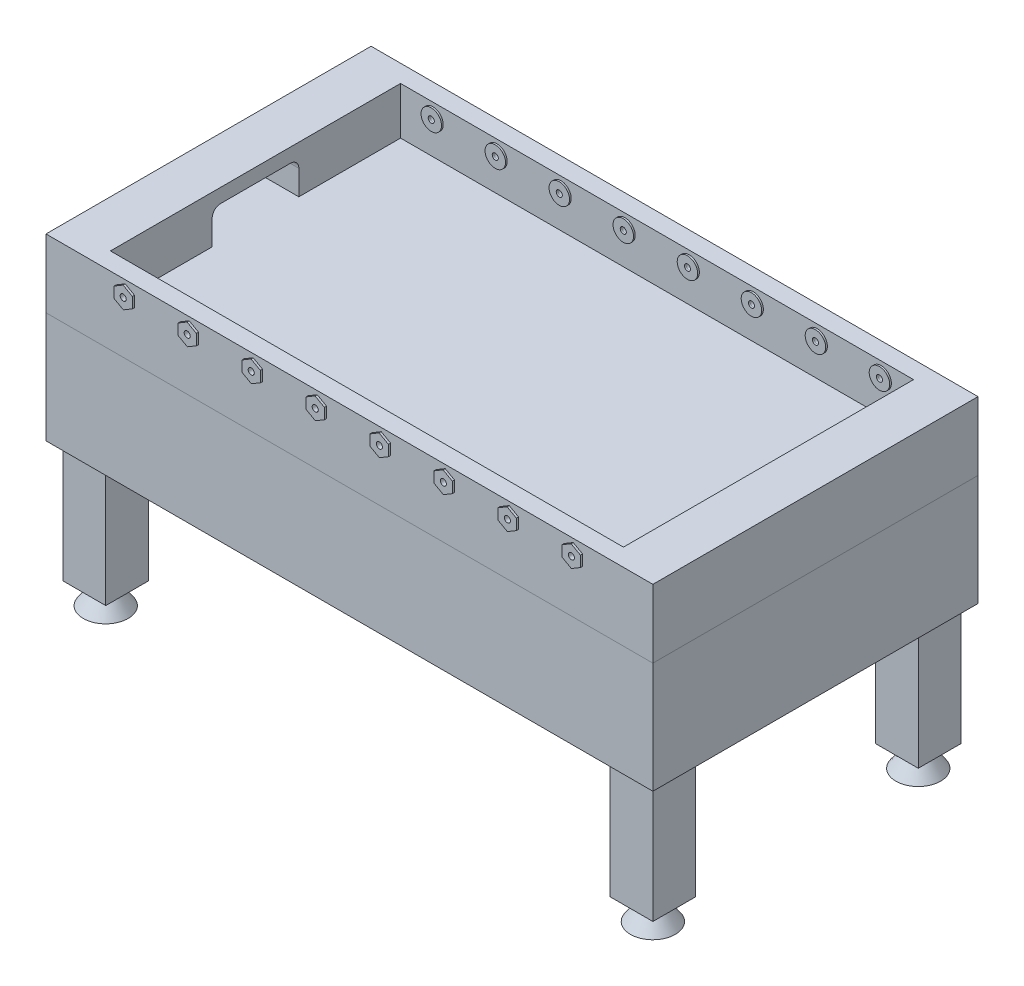
SolidWorks part; units mm, degrees
ref_plane "Front Plane" through (0, 0, 0) normal (0, 0, 1) x (1, 0, 0)
ref_plane "Top Plane" through (0, 0, 0) normal (0, 1, 0) x (1, 0, 0)
ref_plane "Right Plane" through (0, 0, 0) normal (1, 0, 0) x (0, 0, -1)
sketch "스케치1" plane through (0, 0, 0) normal (0, 1, 0) x (1, 0, 0)
  line L1 (711.2, -381) -> (-711.2, -381)
  line L2 (711.2, -381) -> (711.2, 381)
  line L3 (711.2, 381) -> (-711.2, 381)
  line L4 (-711.2, -381) -> (-711.2, 381)
  line L5 (711.2, -381) -> (-711.2, 381) construction
  line L6 (711.2, 381) -> (-711.2, -381) construction
  point P0 (0, 0)
  dimension "D1" = 1422.4
  dimension "D2" = 762
extrude "보스-돌출1" add sketch "스케치1" along normal blind 160
sketch "스케치2" plane through (0, 160, 0) normal (0, 1, 0) x (1, 0, 0)
  line L1 (601.2, -340) -> (-601.2, -340)
  line L2 (601.2, -340) -> (601.2, 340)
  line L3 (601.2, 340) -> (-601.2, 340)
  line L4 (-601.2, -340) -> (-601.2, 340)
  line L5 (601.2, -340) -> (-601.2, 340) construction
  line L6 (601.2, 340) -> (-601.2, -340) construction
  point P0 (0, 0)
  dimension "D1" = 1202.4
  dimension "D2" = 680
extrude "컷-돌출1" cut sketch "스케치2" against normal blind 111
sketch "스케치3" plane through (601.2, 0, 0) normal (-1, 0, 0) x (0, 0, 1)
  line L0 (340, 49) -> (-340, 49) construction
  line L2 (-101.6, 49) -> (-101.6, 127)
  line L3 (-101.6, 127) -> (101.6, 127)
  line L4 (101.6, 49) -> (101.6, 127)
  line L5 (0, 49) -> (101.6, 127) construction
  line L6 (-101.6, 127) -> (0, 49) construction
  line L7 (-148.063, 49) -> (174.1502, 49) construction
  line L8 (-101.6, 49) -> (101.6, 49)
  point P0 (0, 49)
  dimension "D1" = 203.2
extrude "컷-돌출2" cut sketch "스케치3" against normal blind 80
mirror "대칭 복사1" about plane through (0, 0, 0) normal (1, 0, 0) of "컷-돌출2"
sketch "스케치4" plane through (0, 0, -340) normal (0, 0, 1) x (1, 0, 0)
  line L0 (-601.2, 49) -> (601.2, 49) construction
  line L1 (-601.2, 160) -> (-601.2, 49) construction
  line L2 (601.2, 49) -> (601.2, 160) construction
  line L3 (0, -88) -> (0, 88) construction
  circle A0 centre (-525.2, 126.5) radius 24
  circle A1 centre (-375.2, 126.5) radius 24
  circle A2 centre (-225.2, 126.5) radius 24
  circle A3 centre (-75.2, 126.5) radius 24
  circle A4 centre (75.2, 126.5) radius 24
  circle A5 centre (225.2, 126.5) radius 24
  circle A6 centre (375.2, 126.5) radius 24
  circle A7 centre (525.2, 126.5) radius 24
  circle A8 centre (-525.2, 126.5) radius 7.1437
  circle A9 centre (-375.2, 126.5) radius 7.1438
  circle A10 centre (-225.2, 126.5) radius 7.1438
  circle A11 centre (-75.2, 126.5) radius 7.1437
  circle A12 centre (75.2, 126.5) radius 7.1437
  circle A13 centre (225.2, 126.5) radius 7.1438
  circle A14 centre (375.2, 126.5) radius 7.1438
  circle A15 centre (525.2, 126.5) radius 7.1437
  dimension "D3" = 48
  dimension "D4" = 48
  dimension "D6" = 150
  dimension "D8" = 14.2875
  dimension "D9" = 14.2875
  dimension "D10" = 14.2875
  dimension "D11" = 14.2875
  dimension "D1" = 76
  dimension "D2" = 77.5
  dimension "D5" = 150
  dimension "D7" = 150
extrude "보스-돌출2" add sketch "스케치4" along normal blind 4 separate body
mirror "대칭 복사2" about plane through (0, 0, 0) normal (0, 0, 1) of "보스-돌출2"
sketch "스케치5" plane through (0, 0, 0) normal (0, -1, 0) x (1, 0, 0)
  line L1 (711.2, -381) -> (-711.2, -381)
  line L2 (711.2, -381) -> (711.2, 381)
  line L3 (711.2, 381) -> (-711.2, 381)
  line L4 (-711.2, -381) -> (-711.2, 381)
  line L5 (711.2, -381) -> (-711.2, 381) construction
  line L6 (711.2, 381) -> (-711.2, -381) construction
  point P0 (0, 0)
extrude "보스-돌출3" add sketch "스케치5" along normal blind 260 separate body
sketch "스케치6" plane through (0, 0, -340) normal (0, 0, 1) x (1, 0, 0)
  circle A0 centre (-525.2, 126.5) radius 7.1438 construction
  circle A1 centre (-525.2, 126.5) radius 7.1437
  circle A2 centre (525.2, 126.5) radius 7.1438 construction
  circle A3 centre (375.2, 126.5) radius 7.1438 construction
  circle A4 centre (225.2, 126.5) radius 7.1438 construction
  circle A5 centre (-75.2, 126.5) radius 7.1438 construction
  circle A6 centre (-225.2, 126.5) radius 7.1438 construction
  circle A7 centre (-375.2, 126.5) radius 7.1438 construction
  circle A8 centre (525.2, 126.5) radius 7.1437
  circle A9 centre (375.2, 126.5) radius 7.1438
  circle A10 centre (225.2, 126.5) radius 7.1438
  circle A11 centre (-75.2, 126.5) radius 7.1437
  circle A12 centre (-225.2, 126.5) radius 7.1438
  circle A13 centre (-375.2, 126.5) radius 7.1438
  circle A14 centre (75.2, 126.5) radius 7.1438 construction
  circle A15 centre (75.2, 126.5) radius 7.1437
sketch "스케치7" plane through (0, -260, 0) normal (0, -1, 0) x (1, 0, 0)
  line L0 (711.2, 381) -> (-711.2, 381) construction
  line L1 (-691.2, 361) -> (-591.2, 361)
  line L2 (-691.2, 361) -> (-691.2, 261)
  line L3 (-691.2, 261) -> (-591.2, 261)
  line L4 (-591.2, 361) -> (-591.2, 261)
  line L5 (-691.2, 361) -> (-591.2, 261) construction
  line L6 (-691.2, 261) -> (-591.2, 361) construction
  line L7 (-711.2, 381) -> (-711.2, -381) construction
  line L8 (0, -414.92) -> (0, 414.92) construction
  line L9 (691.2, 261) -> (591.2, 261)
  line L10 (591.2, 361) -> (591.2, 261)
  line L11 (691.2, 361) -> (591.2, 361)
  line L12 (691.2, 361) -> (691.2, 261)
  line L13 (414.92, 0) -> (-414.92, 0) construction
  line L14 (691.2, -361) -> (691.2, -261)
  line L15 (691.2, -361) -> (591.2, -361)
  line L16 (591.2, -361) -> (591.2, -261)
  line L17 (691.2, -261) -> (591.2, -261)
  line L18 (-691.2, -261) -> (-591.2, -261)
  line L19 (-591.2, -361) -> (-591.2, -261)
  line L20 (-691.2, -361) -> (-591.2, -361)
  line L21 (-691.2, -361) -> (-691.2, -261)
  point P0 (-641.2, 311)
  dimension "D1" = 100
  dimension "D2" = 100
  dimension "D3" = 70
  dimension "D4" = 70
extrude "보스-돌출4" add sketch "스케치7" along normal blind 284.4
sketch "스케치8" plane through (0, -544.4, 0) normal (0, -1, 0) x (1, 0, 0)
  line L2 (0, -414.92) -> (0, 414.92) construction
  line L3 (414.92, 0) -> (-414.92, 0) construction
  circle A4 centre (-641.2, 311) radius 17.5
  circle A5 centre (641.2, 311) radius 17.5
  circle A6 centre (641.2, -311) radius 17.5
  circle A7 centre (-641.2, -311) radius 17.5
  dimension "D1" = 35
extrude "보스-돌출5" add sketch "스케치8" along normal blind 50 draft 35 draft outward yes
sketch "스케치9" plane through (0, 0, 381) normal (0, 0, 1) x (1, 0, 0)
  line L0 (-353.3752, 114.3066) -> (-353.7278, 139.3042)
  line L1 (-503.3752, 114.3066) -> (-503.7278, 139.3042)
  line L2 (-503.7278, 139.3042) -> (-525.5526, 151.4975)
  line L3 (-525.5526, 151.4975) -> (-547.0248, 138.6934)
  line L4 (-547.0248, 138.6934) -> (-546.6722, 113.6958)
  line L5 (-546.6722, 113.6958) -> (-524.8474, 101.5025)
  line L6 (-524.8474, 101.5025) -> (-503.3752, 114.3066)
  line L7 (-353.7278, 139.3042) -> (-375.5526, 151.4975)
  line L8 (-375.5526, 151.4975) -> (-397.0248, 138.6934)
  line L9 (-397.0248, 138.6934) -> (-396.6722, 113.6958)
  line L10 (-396.6722, 113.6958) -> (-374.8474, 101.5025)
  line L11 (-374.8474, 101.5025) -> (-353.3752, 114.3066)
  line L12 (-203.3752, 114.3066) -> (-203.7278, 139.3042)
  line L13 (-203.7278, 139.3042) -> (-225.5526, 151.4975)
  line L14 (-225.5526, 151.4975) -> (-247.0248, 138.6934)
  line L15 (-247.0248, 138.6934) -> (-246.6722, 113.6958)
  line L16 (-246.6722, 113.6958) -> (-224.8474, 101.5025)
  line L17 (-224.8474, 101.5025) -> (-203.3752, 114.3066)
  line L18 (-53.3752, 114.3066) -> (-53.7278, 139.3042)
  line L19 (-53.7278, 139.3042) -> (-75.5526, 151.4975)
  line L20 (-75.5526, 151.4975) -> (-97.0248, 138.6934)
  line L21 (-97.0248, 138.6934) -> (-96.6722, 113.6958)
  line L22 (-96.6722, 113.6958) -> (-74.8474, 101.5025)
  line L23 (-74.8474, 101.5025) -> (-53.3752, 114.3066)
  line L24 (96.6248, 114.3066) -> (96.2722, 139.3042)
  line L25 (96.2722, 139.3042) -> (74.4474, 151.4975)
  line L26 (74.4474, 151.4975) -> (52.9752, 138.6934)
  line L27 (52.9752, 138.6934) -> (53.3278, 113.6958)
  line L28 (53.3278, 113.6958) -> (75.1526, 101.5025)
  line L29 (75.1526, 101.5025) -> (96.6248, 114.3066)
  line L30 (246.6248, 114.3066) -> (246.2722, 139.3042)
  line L31 (246.2722, 139.3042) -> (224.4474, 151.4975)
  line L32 (224.4474, 151.4975) -> (202.9752, 138.6934)
  line L33 (202.9752, 138.6934) -> (203.3278, 113.6958)
  line L34 (203.3278, 113.6958) -> (225.1526, 101.5025)
  line L35 (225.1526, 101.5025) -> (246.6248, 114.3066)
  line L36 (396.6248, 114.3066) -> (396.2722, 139.3042)
  line L37 (396.2722, 139.3042) -> (374.4474, 151.4975)
  line L38 (374.4474, 151.4975) -> (352.9752, 138.6934)
  line L39 (352.9752, 138.6934) -> (353.3278, 113.6958)
  line L40 (353.3278, 113.6958) -> (375.1526, 101.5025)
  line L41 (375.1526, 101.5025) -> (396.6248, 114.3066)
  line L42 (546.6248, 114.3066) -> (546.2722, 139.3042)
  line L43 (546.2722, 139.3042) -> (524.4474, 151.4975)
  line L44 (524.4474, 151.4975) -> (502.9752, 138.6934)
  line L45 (502.9752, 138.6934) -> (503.3278, 113.6958)
  line L46 (503.3278, 113.6958) -> (525.1526, 101.5025)
  line L47 (525.1526, 101.5025) -> (546.6248, 114.3066)
  circle A0 centre (-525.2, 126.5) radius 21.6506 construction
  circle A1 centre (-375.2, 126.5) radius 21.6506 construction
  circle A2 centre (-225.2, 126.5) radius 21.6506 construction
  circle A3 centre (-75.2, 126.5) radius 21.6506 construction
  circle A4 centre (74.8, 126.5) radius 21.6506 construction
  circle A5 centre (224.8, 126.5) radius 21.6506 construction
  circle A6 centre (374.8, 126.5) radius 21.6506 construction
  circle A7 centre (524.8, 126.5) radius 21.6506 construction
  dimension "D1" = 25
  dimension "D2" = 8
extrude "보스-돌출6" add sketch "스케치9" along normal blind 5
mirror "대칭 복사3" about plane through (0, 0, 0) normal (0, 0, 1) of "보스-돌출6"
sketch "스케치10" plane through (0, 0, -340) normal (0, 0, 1) x (1, 0, 0)
  circle A0 centre (525.2, 126.5) radius 7.1438 construction
  circle A1 centre (375.2, 126.5) radius 7.1438 construction
  circle A2 centre (225.2, 126.5) radius 7.1438 construction
  circle A3 centre (75.2, 126.5) radius 7.1438 construction
  circle A4 centre (-75.2, 126.5) radius 7.1438 construction
  circle A5 centre (-225.2, 126.5) radius 7.1438 construction
  circle A6 centre (-375.2, 126.5) radius 7.1438 construction
  circle A7 centre (-525.2, 126.5) radius 7.1438 construction
  circle A8 centre (525.2, 126.5) radius 7.1437
  circle A9 centre (375.2, 126.5) radius 7.1438
  circle A10 centre (225.2, 126.5) radius 7.1438
  circle A11 centre (75.2, 126.5) radius 7.1437
  circle A12 centre (-75.2, 126.5) radius 7.1437
  circle A13 centre (-225.2, 126.5) radius 7.1438
  circle A14 centre (-375.2, 126.5) radius 7.1438
  circle A15 centre (-525.2, 126.5) radius 7.1437
extrude "컷-돌출4" cut sketch "스케치10" against normal through all both and the other way through all
sketch "스케치11" plane through (0, 0, -381) normal (0, 0, -1) x (-1, 0, 0)
  line L0 (-81, 0) -> (81, 0)
  line L2 (-81, 0) -> (-81, -85)
  line L3 (-81, -85) -> (81, -85)
  line L4 (81, 0) -> (81, -85)
  line L5 (0, 0) -> (81, -85) construction
  line L6 (-81, -85) -> (0, 0) construction
  point P0 (0, 0)
  dimension "D1" = 162
  dimension "D2" = 85
extrude "컷-돌출5" cut sketch "스케치11" against normal up to surface (381 mm away) and the other way through all up to plane "Front Plane"
sketch "스케치14" plane through (-81, 0, 0) normal (1, 0, 0) x (0, 0, -1)
  line L0 (0, -85) -> (361, -108.114)
  line L3 (361, -85) -> (0, -85)
  line L4 (381, 0) -> (0, 0)
  line L5 (0, 0) -> (0, -85)
  line L6 (0, -85) -> (381, -85)
  line L7 (381, -85) -> (381, 0)
  line L8 (381, 0) -> (0, 0) construction
  line L9 (0, 0) -> (0, -85) construction
  line L10 (0, -85) -> (361, -85) construction
  line L11 (381, -85) -> (381, 0) construction
  line L12 (361, -85) -> (361, -108.114)
  dimension "D2" = 23.114
  dimension "D3" = 20
  dimension "D1" = 0
extrude "컷-돌출6" cut sketch "스케치14" along normal up to surface (162 mm away) up to face at (81, -42.5, -190.5)
sketch "스케치15" plane through (81, 0, 0) normal (-1, 0, 0) x (0, 0, 1)
  line L0 (-361, 0) -> (-361, -108.114)
  line L3 (-361, 0) -> (0, 0)
  line L4 (0, -85) -> (0, 0)
  line L5 (-361, -108.114) -> (0, -85)
  line L6 (-381, -85) -> (-361, -85)
  line L7 (-361, -85) -> (-361, -108.114)
  line L8 (-361, -108.114) -> (0, -85)
  line L9 (0, -85) -> (0, 0)
  line L10 (0, 0) -> (-381, 0)
  line L11 (-381, 0) -> (-381, -85)
  line L12 (-381, -85) -> (-361, -85) construction
  line L13 (-361, -85) -> (-361, -108.114) construction
  line L14 (-361, -108.114) -> (0, -85) construction
  line L15 (0, -85) -> (0, 0) construction
  line L16 (0, 0) -> (-381, 0) construction
  line L17 (-381, 0) -> (-381, -85) construction
  dimension "D1" = 0
extrude "컷-돌출7" cut sketch "스케치15" against normal blind 10
mirror "대칭 복사4" about plane through (0, 0, 0) normal (1, 0, 0) of "컷-돌출7"
fillet "필렛1" radius 20 4 edges at (-641.2, 127, 101.6) (-641.2, 127, -101.6) (641.2, 127, 101.6) (641.2, 127, -101.6)
